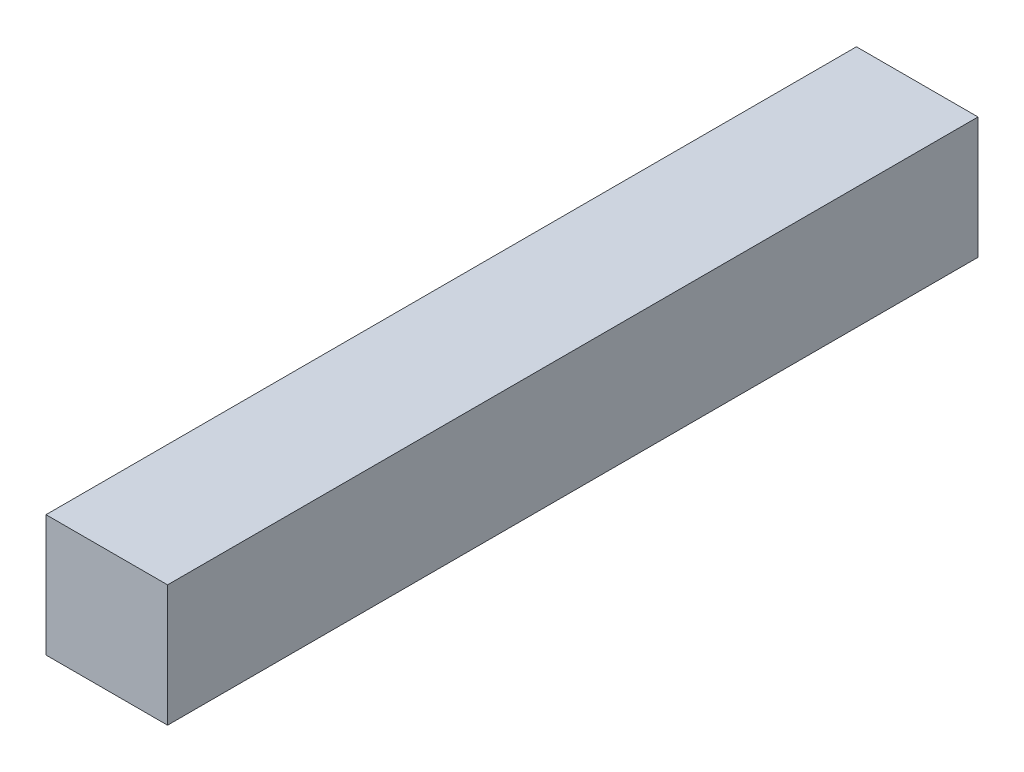
SolidWorks part; units mm, degrees
ref_plane "Front Plane" through (0, 0, 0) normal (0, 0, 1) x (1, 0, 0)
ref_plane "Top Plane" through (0, 0, 0) normal (0, 1, 0) x (1, 0, 0)
ref_plane "Right Plane" through (0, 0, 0) normal (1, 0, 0) x (0, 0, -1)
sketch "Sketch1" plane through (0, 0, 0) normal (0, 0, 1) x (1, 0, 0)
  line L1 (0, 0) -> (45, 0)
  line L2 (0, 0) -> (0, 45)
  line L3 (0, 45) -> (45, 45)
  line L4 (45, 0) -> (45, 45)
  dimension "D1" = 45
  dimension "D2" = 45
extrude "Boss-Extrude1" add sketch "Sketch1" along normal blind 300
